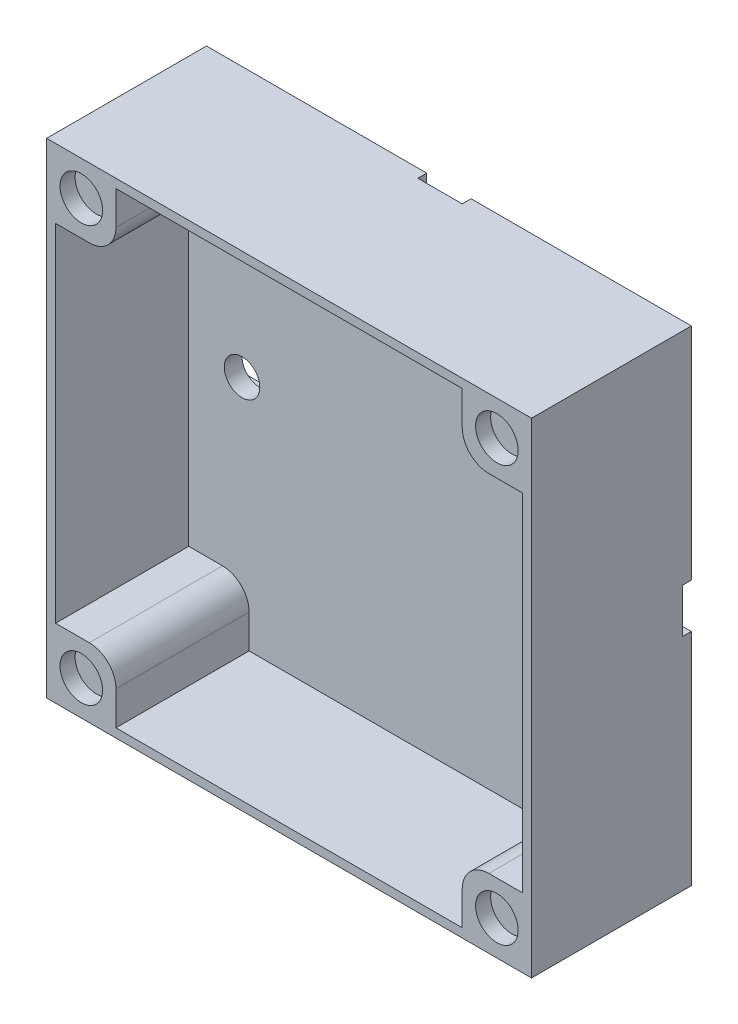
SolidWorks part; units mm, degrees
ref_plane "Přední rovina" through (0, 0, 0) normal (0, 0, 1) x (1, 0, 0)
ref_plane "Horní rovina" through (0, 0, 0) normal (0, 1, 0) x (1, 0, 0)
ref_plane "Pravá rovina" through (0, 0, 0) normal (1, 0, 0) x (0, 0, -1)
sketch "Skica1" plane through (0, 0, 0) normal (0, 0, 1) x (1, 0, 0)
  line L1 (27.3, 27.3) -> (-27.3, 27.3)
  line L2 (27.3, 27.3) -> (27.3, -27.3)
  line L3 (27.3, -27.3) -> (-27.3, -27.3)
  line L4 (-27.3, 27.3) -> (-27.3, -27.3)
  line L5 (27.3, 27.3) -> (-27.3, -27.3) construction
  line L6 (27.3, -27.3) -> (-27.3, 27.3) construction
  point P0 (0, 0)
  point P5 (-27.5, 0)
  point P11 (4.5, 0)
  dimension "D1" = 54.6
  dimension "D2" = 54.6
extrude "Přidat vysunutím2" add sketch "Skica1" along normal blind 3 contours L2 L1 L4 L3
sketch "Skica5" plane through (0, 0, 0) normal (0, 0, -1) x (-1, 0, 0)
  line L0 (-27.3, 27.3) -> (27.3, 27.3) construction
  line L5 (2.5, 27.3) -> (-2.5, 27.3)
  line L10 (27.3, 27.3) -> (27.3, -27.3) construction
  line L11 (-27.3, 2.5) -> (27.3, 2.5)
  line L12 (-27.3, 2.5) -> (-27.3, -2.5)
  line L13 (-27.3, -2.5) -> (27.3, -2.5)
  line L14 (27.3, 2.5) -> (27.3, -2.5)
  line L15 (-27.3, 2.5) -> (27.3, -2.5) construction
  line L16 (-27.3, -2.5) -> (27.3, 2.5) construction
  line L17 (2.5, 27.3) -> (2.5, 2.5)
  line L18 (2.5, 2.5) -> (-2.5, 2.5)
  line L19 (-2.5, 27.3) -> (-2.5, 2.5)
  line L20 (-27.3, 27.3) -> (-27.3, -27.3) construction
  point P0 (0, 0)
  dimension "D1" = 5
  dimension "D2" = 24.8
  dimension "D3" = 5
  dimension "D4" = 24.8
extrude "Odebrat vysunutím3" cut sketch "Skica5" against normal blind 1 contours L11 L14 L13 L12 | L17 L5 L19 L18
sketch "Skica14" plane through (0, 0, 3) normal (0, 0, 1) x (1, 0, 0)
  line L1 (-27.3, 27.3) -> (27.3, 27.3)
  line L2 (-27.3, 27.3) -> (-27.3, -27.3)
  line L3 (-27.3, -27.3) -> (27.3, -27.3)
  line L4 (27.3, 27.3) -> (27.3, -27.3)
  line L5 (-26.3, 26.3) -> (26.3, 26.3)
  line L6 (-26.3, 26.3) -> (-26.3, -27.3)
  line L7 (-26.3, -27.3) -> (26.3, -27.3)
  line L8 (26.3, 26.3) -> (26.3, -27.3)
  line L9 (-26.3, -27.3) -> (26.3, -27.3)
  line L10 (-26.3, -27.3) -> (-26.3, -26.3)
  line L11 (-26.3, -26.3) -> (26.3, -26.3)
  line L12 (26.3, -27.3) -> (26.3, -26.3)
  line M13 (-27.3, -27.3) -> (27.3, -27.3)
  line M14 (27.3, -27.3) -> (27.3, 27.3)
  line M15 (27.3, 27.3) -> (-27.3, 27.3)
  line M16 (-27.3, 27.3) -> (-27.3, -27.3)
  dimension "D1" = 1
  dimension "D2" = 1
  dimension "D3" = 1
  dimension "D4" = 0
  dimension "D5" = 1
  dimension "D6" = 52.6
extrude "Přidat vysunutím9" add sketch "Skica14" along normal blind 15 contours L5 L8 L6 M13 M14 M15 M16 | L10 L9 L12 L11
sketch "Skica17" plane through (0, 0, 1) normal (0, 0, -1) x (-1, 0, 0)
  line L0 (-27.3, 2.5) -> (-27.3, -2.5) construction
  line L2 (27.3, 2.5) -> (27.3, -2.5) construction
  line L4 (2.5, 27.3) -> (-2.5, 27.3) construction
  circle A0 centre (-20.3, 0) radius 2
  circle A1 centre (20.3, 0) radius 2
  circle A2 centre (0, 20.3) radius 2
  dimension "D1" = 4
  dimension "D2" = 4
  dimension "D6" = 7
  dimension "D4" = 4
  dimension "D3" = 7
  dimension "D5" = 7
extrude "Odebrat vysunutím8" cut sketch "Skica17" against normal blind 7 contours A2 | A1 | A0
sketch "Skica19" plane through (0, 0, 0) normal (0, 0, -1) x (-1, 0, 0)
  line L1 (-27.3, 27.3) -> (-19.5, 27.3)
  line L2 (-27.3, 27.3) -> (-27.3, 19.5)
  line L3 (-27.3, 19.5) -> (-19.5, 19.5)
  line L4 (-19.5, 27.3) -> (-19.5, 19.5)
  line L5 (27.3, 27.3) -> (19.5, 27.3)
  line L6 (27.3, 27.3) -> (27.3, 19.5)
  line L7 (27.3, 19.5) -> (19.5, 19.5)
  line L8 (19.5, 27.3) -> (19.5, 19.5)
  line L9 (-27.3, -27.3) -> (-19.5, -27.3)
  line L10 (-27.3, -27.3) -> (-27.3, -19.5)
  line L11 (-27.3, -19.5) -> (-19.5, -19.5)
  line L12 (-19.5, -27.3) -> (-19.5, -19.5)
  line L13 (27.3, -27.3) -> (19.5, -27.3)
  line L14 (27.3, -27.3) -> (27.3, -19.5)
  line L15 (27.3, -19.5) -> (19.5, -19.5)
  line L16 (19.5, -27.3) -> (19.5, -19.5)
  dimension "D1" = 7.8
  dimension "D2" = 7.8
  dimension "D3" = 7.8
  dimension "D4" = 7.8
extrude "Přidat vysunutím10" add sketch "Skica19" against normal blind 18
sketch "Skica20" plane through (0, 0, 18) normal (0, 0, 1) x (1, 0, 0)
  line L0 (-27.3, -27.3) -> (27.3, -27.3) construction
  line L1 (-19.5, -26.3) -> (-19.5, -19.5) construction
  line L2 (-27.3, 27.3) -> (-27.3, -27.3) construction
  line L3 (27.3, 27.3) -> (-27.3, 27.3) construction
  line L4 (27.3, -27.3) -> (27.3, 27.3) construction
  line L5 (-27.3, -27.3) -> (27.3, -27.3) construction
  circle A0 centre (-23.4, -23.4) radius 2.4
  circle A1 centre (-23.4, 23.4) radius 2.4
  circle A2 centre (23.4003, 23.4) radius 2.4
  circle A3 centre (23.4003, -23.4) radius 2.4
  dimension "D1" = 4.8
  dimension "D4" = 4.8
  dimension "D5" = 3.9
  dimension "D7" = 4.8
  dimension "D10" = 4.8
  dimension "D2" = 3.9
  dimension "D3" = 3.9
  dimension "D6" = 3.9
  dimension "D8" = 3.8997
  dimension "D9" = 3.9
  dimension "D11" = 3.9
  dimension "D12" = 3.8997
extrude "Odebrat vysunutím9" cut sketch "Skica20" against normal blind 1.7
fillet "Zaoblit1" radius 3 4 edges at (19.5, 19.5, 10.5) (19.5, -19.5, 10.5) (-19.5, -19.5, 10.5) (-19.5, 19.5, 10.5)
